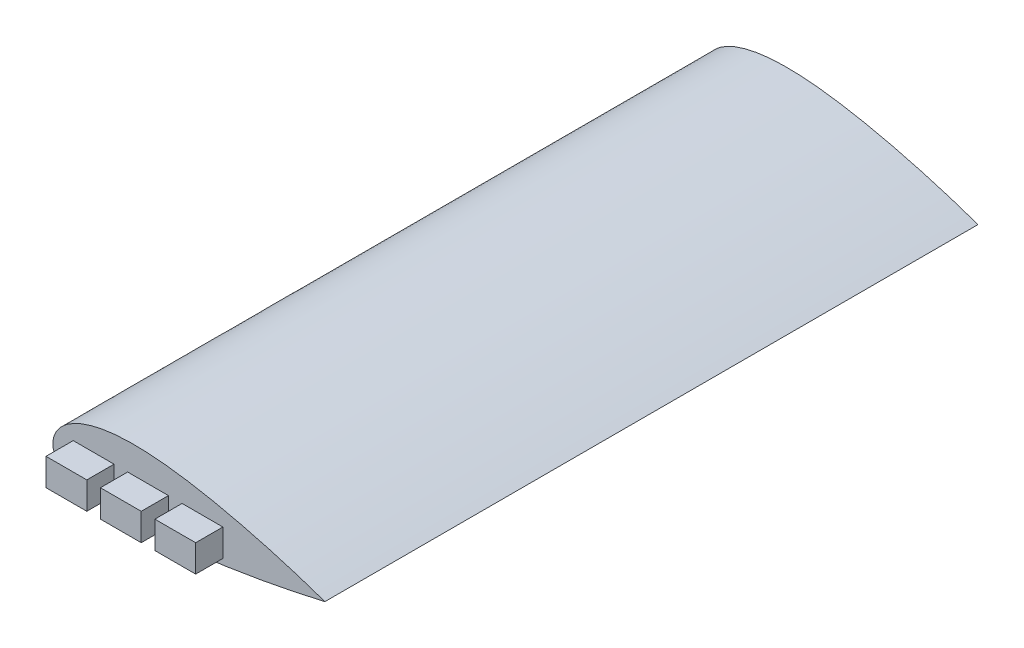
SolidWorks part; units mm, degrees
ref_plane "Front Plane" through (0, 0, 0) normal (0, 0, 1) x (1, 0, 0)
ref_plane "Top Plane" through (0, 0, 0) normal (0, 1, 0) x (1, 0, 0)
ref_plane "Right Plane" through (0, 0, 0) normal (1, 0, 0) x (0, 0, -1)
sketch "Sketch1" plane through (0, 0, 0) normal (0, 0, 1) x (1, 0, 0)
  spline S0 degree 4 poles (0, 0) (0.0009, 0.3297) (0.0295, 0.9275) (0.1439, 1.7967) (0.437, 2.9181) (0.8549, 3.9907) (1.4315, 5.0756) (2.1923, 6.1773) (3.2003, 7.33) (4.4959, 8.5106) (6.154, 9.7149) (8.2741, 10.9292) (10.957, 12.1146) (14.1477, 13.1525) (18.0405, 14.0363) (23.1343, 14.7366) (29.2357, 15.0274) (35.338, 14.8248) (41.1011, 14.3138) (46.841, 13.5968) (51.6037, 12.8505) (56.3456, 11.9834) (61.0671, 11.0139) (64.8328, 10.183) (68.5865, 9.3015) (72.3294, 8.3726) (76.0598, 7.3994) (79.3157, 6.5093) (82.096, 5.721) (84.4127, 5.0444) (86.2537, 4.4957) (88.1107, 3.9294) (89.9289, 3.3646) (91.806, 2.7666) (93.571, 2.1956) (95.5202, 1.5463) (97.1384, 1.0009) (99.1531, 0.3002) (100.3626, -0.127) (101.915, -0.6848) (103.1337, -1.1307) (104.3912, -1.5976) (105.6393, -2.0687) (106.8855, -2.5467) (108.1291, -3.0316) (109.0597, -3.4006) (109.6792, -3.6489) (109.9887, -3.7737) knots 0 0 0 0 0 0.011046 0.020082 0.029326 0.038802 0.04958 0.06121 0.074146 0.090071 0.108265 0.129827 0.155965 0.188307 0.220649 0.263591 0.328276 0.39296 0.425303 0.457645 0.522329 0.554672 0.587014 0.619356 0.651699 0.684041 0.716383 0.748725 0.764896 0.781068 0.797239 0.81341 0.829581 0.845752 0.861923 0.878094 0.894265 0.910437 0.921632 0.932827 0.944023 0.955218 0.966414 0.977609 0.988805 1 1 1 1 1 construction
  spline S1 degree 4 poles (0, 0) (0.0009, 0.3297) (0.0295, 0.9275) (0.1439, 1.7967) (0.437, 2.9181) (0.8549, 3.9907) (1.4315, 5.0756) (2.1923, 6.1773) (3.2003, 7.33) (4.4959, 8.5106) (6.154, 9.7149) (8.2741, 10.9292) (10.957, 12.1146) (14.1477, 13.1525) (18.0405, 14.0363) (23.1343, 14.7366) (29.2357, 15.0274) (35.338, 14.8248) (41.1011, 14.3138) (46.841, 13.5968) (51.6037, 12.8505) (56.3456, 11.9834) (61.0671, 11.0139) (64.8328, 10.183) (68.5865, 9.3015) (72.3294, 8.3726) (76.0598, 7.3994) (79.3157, 6.5093) (82.096, 5.721) (84.4127, 5.0444) (86.2537, 4.4957) (88.1107, 3.9294) (89.9289, 3.3646) (91.806, 2.7666) (93.571, 2.1956) (95.5202, 1.5463) (97.1383, 1.0009) (98.7751, 0.4317) (99.5867, 0.1465) (100.0002, 0) knots 0 0 0 0 0 0.011046 0.020082 0.029326 0.038802 0.04958 0.06121 0.074146 0.090071 0.108265 0.129827 0.155965 0.188307 0.220649 0.263591 0.328276 0.39296 0.425303 0.457645 0.522329 0.554672 0.587014 0.619356 0.651699 0.684041 0.716383 0.748725 0.764896 0.781068 0.797239 0.81341 0.829581 0.845752 0.861923 0.878094 0.894265 0.910434 0.910434 0.910434 0.910434 0.910434
  spline S2 degree 4 poles (0, 0) (0.0003, -0.1693) (0.016, -0.4614) (0.0775, -0.8851) (0.2333, -1.4356) (0.4512, -1.9609) (0.763, -2.5157) (1.1968, -3.1118) (1.8009, -3.7667) (2.6459, -4.4954) (3.845, -5.3152) (5.5202, -6.2106) (7.8905, -7.1807) (10.9471, -8.0963) (15.4296, -9.0396) (21.208, -9.73) (27.9775, -10.0275) (35.6486, -9.8891) (42.3469, -9.4657) (48.0748, -8.9399) (53.7915, -8.3061) (59.4968, -7.5766) (65.1885, -6.7461) (70.8667, -5.8302) (75.5899, -5.0142) (79.3624, -4.3307) (82.6596, -3.7058) (85.4801, -3.1515) (87.5962, -2.7233) (89.0005, -2.4341) (90.1811, -2.1872) (91.104, -1.9926) (92.3051, -1.7354) (93.6554, -1.4439) (95.3898, -1.0596) (97.1027, -0.6748) (99.4365, -0.1347) (101.1191, 0.2637) (103.9947, 0.9599) (105.7889, 1.4169) (107.9207, 1.9617) (109.0082, 2.2534) (109.6995, 2.4359) (109.9984, 2.5166) knots 0 0 0 0 0 0.005887 0.010193 0.014867 0.019889 0.025655 0.032315 0.040498 0.050865 0.064448 0.082823 0.106556 0.139954 0.175459 0.242256 0.309053 0.375849 0.442646 0.476045 0.509443 0.57624 0.643037 0.676435 0.709833 0.743232 0.77663 0.793329 0.810028 0.818378 0.826728 0.835077 0.843427 0.860126 0.876825 0.893524 0.910224 0.932668 0.955112 0.977556 0.988778 1 1 1 1 1 construction
  spline S3 degree 4 poles (0, 0) (0.0003, -0.1693) (0.016, -0.4614) (0.0775, -0.8851) (0.2333, -1.4356) (0.4512, -1.9609) (0.763, -2.5157) (1.1968, -3.1118) (1.8009, -3.7667) (2.6459, -4.4954) (3.845, -5.3152) (5.5202, -6.2106) (7.8905, -7.1807) (10.9471, -8.0963) (15.4296, -9.0396) (21.208, -9.73) (27.9775, -10.0275) (35.6486, -9.8891) (42.3469, -9.4657) (48.0748, -8.9399) (53.7915, -8.3061) (59.4968, -7.5766) (65.1885, -6.7461) (70.8667, -5.8302) (75.5899, -5.0142) (79.3624, -4.3307) (82.6596, -3.7058) (85.4801, -3.1515) (87.5962, -2.7233) (89.0005, -2.4341) (90.1811, -2.1872) (91.104, -1.9926) (92.3051, -1.7354) (93.6554, -1.4439) (95.3898, -1.0596) (97.1027, -0.6748) (98.7145, -0.3018) (99.5756, -0.1002) (100.0002, 0) knots 0 0 0 0 0 0.005887 0.010193 0.014867 0.019889 0.025655 0.032315 0.040498 0.050865 0.064448 0.082823 0.106556 0.139954 0.175459 0.242256 0.309053 0.375849 0.442646 0.476045 0.509443 0.57624 0.643037 0.676435 0.709833 0.743232 0.77663 0.793329 0.810028 0.818378 0.826728 0.835077 0.843427 0.860126 0.876825 0.893524 0.910224 0.910224 0.910224 0.910224 0.910224
sketch "Sketch2" plane through (0, 0, 0) normal (0, 1, 0) x (1, 0, 0)
  line L1 (0, 0) -> (0, -250) construction
  line L2 (0, -250) -> (50, -500) construction
  spline S0 degree 2 poles (0, 0) (0, -250) (50, -500) knots 0 0 0 1 1 1
  dimension "D1" = 250
  dimension "D2" = 250
  dimension "D3" = 50
ref_plane "Plane2" through (0, 0, 500) normal (0, 0, 1) x (1, 0, 0)
sketch "Sketch5" plane through (0, 0, 500) normal (0, 0, 1) x (1, 0, 0)
  spline S0 degree 4 poles (44.9961, 0) (44.997, 0.3297) (45.0257, 0.9275) (45.14, 1.7967) (45.4332, 2.9181) (45.851, 3.9907) (46.4276, 5.0756) (47.1884, 6.1773) (48.1965, 7.33) (49.4921, 8.5106) (51.1502, 9.7149) (53.2702, 10.9292) (55.9531, 12.1146) (59.1438, 13.1525) (63.0366, 14.0363) (68.1305, 14.7366) (74.2318, 15.0274) (80.3341, 14.8248) (86.0972, 14.3138) (91.8371, 13.5968) (96.5999, 12.8505) (101.3417, 11.9834) (106.0633, 11.0139) (109.8289, 10.183) (113.5826, 9.3015) (117.3256, 8.3726) (121.0559, 7.3994) (124.3119, 6.5093) (127.0921, 5.721) (129.4089, 5.0444) (131.2499, 4.4957) (133.1069, 3.9294) (134.9251, 3.3646) (136.8022, 2.7666) (138.5672, 2.1956) (140.5163, 1.5463) (142.1345, 1.0009) (144.1492, 0.3002) (145.3587, -0.127) (146.9111, -0.6848) (148.1299, -1.1307) (149.3874, -1.5976) (150.6354, -2.0687) (151.8817, -2.5467) (153.1253, -3.0316) (154.0559, -3.4006) (154.6753, -3.6489) (154.9848, -3.7737) knots 0 0 0 0 0 0.011046 0.020082 0.029326 0.038802 0.04958 0.06121 0.074146 0.090071 0.108265 0.129827 0.155965 0.188307 0.220649 0.263591 0.328276 0.39296 0.425303 0.457645 0.522329 0.554672 0.587014 0.619356 0.651699 0.684041 0.716383 0.748725 0.764896 0.781068 0.797239 0.81341 0.829581 0.845752 0.861923 0.878094 0.894265 0.910437 0.921632 0.932827 0.944023 0.955218 0.966414 0.977609 0.988805 1 1 1 1 1 construction
  spline S1 degree 4 poles (44.9961, 0) (44.997, 0.3297) (45.0257, 0.9275) (45.14, 1.7967) (45.4332, 2.9181) (45.851, 3.9907) (46.4276, 5.0756) (47.1884, 6.1773) (48.1965, 7.33) (49.4921, 8.5106) (51.1502, 9.7149) (53.2702, 10.9292) (55.9531, 12.1146) (59.1438, 13.1525) (63.0366, 14.0363) (68.1305, 14.7366) (74.2318, 15.0274) (80.3341, 14.8248) (86.0972, 14.3138) (91.8371, 13.5968) (96.5999, 12.8505) (101.3417, 11.9834) (106.0633, 11.0139) (109.8289, 10.183) (113.5826, 9.3015) (117.3256, 8.3726) (121.0559, 7.3994) (124.3119, 6.5093) (127.0921, 5.721) (129.4089, 5.0444) (131.2499, 4.4957) (133.1069, 3.9294) (134.9251, 3.3646) (136.8022, 2.7666) (138.5672, 2.1956) (140.5163, 1.5463) (142.1344, 1.0009) (143.7713, 0.4317) (144.5828, 0.1465) (144.9964, 0) knots 0 0 0 0 0 0.011046 0.020082 0.029326 0.038802 0.04958 0.06121 0.074146 0.090071 0.108265 0.129827 0.155965 0.188307 0.220649 0.263591 0.328276 0.39296 0.425303 0.457645 0.522329 0.554672 0.587014 0.619356 0.651699 0.684041 0.716383 0.748725 0.764896 0.781068 0.797239 0.81341 0.829581 0.845752 0.861923 0.878094 0.894265 0.910434 0.910434 0.910434 0.910434 0.910434 construction
  spline S2 degree 4 poles (44.9961, 0) (44.9964, -0.1693) (45.0121, -0.4614) (45.0736, -0.8851) (45.2294, -1.4356) (45.4474, -1.9609) (45.7592, -2.5157) (46.193, -3.1118) (46.7971, -3.7667) (47.642, -4.4954) (48.8411, -5.3152) (50.5163, -6.2106) (52.8866, -7.1807) (55.9432, -8.0963) (60.4257, -9.0396) (66.2041, -9.73) (72.9737, -10.0275) (80.6447, -9.8891) (87.343, -9.4657) (93.071, -8.9399) (98.7876, -8.3061) (104.493, -7.5766) (110.1846, -6.7461) (115.8628, -5.8302) (120.586, -5.0142) (124.3586, -4.3307) (127.6557, -3.7058) (130.4762, -3.1515) (132.5924, -2.7233) (133.9966, -2.4341) (135.1772, -2.1872) (136.1002, -1.9926) (137.3012, -1.7354) (138.6515, -1.4439) (140.3859, -1.0596) (142.0988, -0.6748) (144.4327, -0.1347) (146.1152, 0.2637) (148.9908, 0.9599) (150.7851, 1.4169) (152.9168, 1.9617) (154.0043, 2.2534) (154.6957, 2.4359) (154.9945, 2.5166) knots 0 0 0 0 0 0.005887 0.010193 0.014867 0.019889 0.025655 0.032315 0.040498 0.050865 0.064448 0.082823 0.106556 0.139954 0.175459 0.242256 0.309053 0.375849 0.442646 0.476045 0.509443 0.57624 0.643037 0.676435 0.709833 0.743232 0.77663 0.793329 0.810028 0.818378 0.826728 0.835077 0.843427 0.860126 0.876825 0.893524 0.910224 0.932668 0.955112 0.977556 0.988778 1 1 1 1 1 construction
  spline S3 degree 4 poles (44.9961, 0) (44.9964, -0.1693) (45.0121, -0.4614) (45.0736, -0.8851) (45.2294, -1.4356) (45.4474, -1.9609) (45.7592, -2.5157) (46.193, -3.1118) (46.7971, -3.7667) (47.642, -4.4954) (48.8411, -5.3152) (50.5163, -6.2106) (52.8866, -7.1807) (55.9432, -8.0963) (60.4257, -9.0396) (66.2041, -9.73) (72.9737, -10.0275) (80.6447, -9.8891) (87.343, -9.4657) (93.071, -8.9399) (98.7876, -8.3061) (104.493, -7.5766) (110.1846, -6.7461) (115.8628, -5.8302) (120.586, -5.0142) (124.3586, -4.3307) (127.6557, -3.7058) (130.4762, -3.1515) (132.5924, -2.7233) (133.9966, -2.4341) (135.1772, -2.1872) (136.1002, -1.9926) (137.3012, -1.7354) (138.6515, -1.4439) (140.3859, -1.0596) (142.0988, -0.6748) (143.7106, -0.3018) (144.5718, -0.1002) (144.9964, 0) knots 0 0 0 0 0 0.005887 0.010193 0.014867 0.019889 0.025655 0.032315 0.040498 0.050865 0.064448 0.082823 0.106556 0.139954 0.175459 0.242256 0.309053 0.375849 0.442646 0.476045 0.509443 0.57624 0.643037 0.676435 0.709833 0.743232 0.77663 0.793329 0.810028 0.818378 0.826728 0.835077 0.843427 0.860126 0.876825 0.893524 0.910224 0.910224 0.910224 0.910224 0.910224 construction
  spline S4 degree 1 poles (50, 0.1659) (125.4884, 0.9751) knots 0 0 1 1 construction
  spline S5 degree 1 poles (50, 0.1659) (125.4884, 0.9751) knots 0 0 1 1 construction
  spline S6 degree 3 poles (50, 0.1659) (50.0179, 0.6032) (50.1757, 1.4567) (50.8242, 2.7316) (51.9666, 4.0552) (54.0561, 5.71) (57.4359, 7.406) (62.0985, 8.7726) (67.0831, 9.581) (73.966, 10.0492) (82.8075, 9.7192) (93.5157, 8.3656) (107.7971, 5.6881) (118.4649, 2.9873) (125.4884, 0.9751) knots 0.003107 0.003107 0.003107 0.003107 0.026472 0.049837 0.073202 0.096568 0.143298 0.190028 0.236758 0.283489 0.376949 0.47041 0.56387 0.750791 0.750791 0.750791 0.750791
  spline S7 degree 3 poles (125.4884, 0.9751) (118.8048, -0.2943) (108.7202, -1.9955) (95.2701, -3.722) (85.1977, -4.6498) (76.8507, -4.9962) (70.2537, -4.8947) (65.3724, -4.5831) (61.4032, -4.0773) (58.338, -3.4825) (56.1227, -2.928) (54.0329, -2.2507) (52.4618, -1.576) (51.3904, -0.9852) (50.7151, -0.5321) (50.3053, -0.1828) (50.0857, 0.053) (50.0309, 0.1225) (50, 0.1659) knots 0.025551 0.025551 0.025551 0.025551 0.205368 0.295277 0.385186 0.475094 0.520049 0.565003 0.609957 0.632435 0.654912 0.677389 0.699866 0.711105 0.722343 0.733582 0.739201 0.74482 0.74482 0.74482 0.74482
  spline S8 degree 1 poles (57.6356, 1.8665) (100.2923, 1.9767) knots 0 0 1 1 construction
  spline S9 degree 1 poles (57.6356, 1.8665) (100.2923, 1.9767) knots 0 0 1 1 construction
  spline S10 degree 3 poles (57.6356, 1.8665) (57.9231, 2.0151) (58.4925, 2.2874) (59.782, 2.82) (61.5543, 3.4029) (63.8869, 3.9672) (67.1912, 4.5347) (71.5938, 4.9175) (77.127, 4.9346) (82.8116, 4.5908) (88.5912, 3.9528) (94.4204, 3.0772) (98.3432, 2.3598) (100.2923, 1.9767) knots 0.118651 0.118651 0.118651 0.118651 0.131754 0.144858 0.171065 0.197272 0.223479 0.275893 0.328307 0.380721 0.433135 0.485549 0.537964 0.537964 0.537964 0.537964
  spline S11 degree 3 poles (100.2923, 1.9767) (98.4159, 1.7345) (94.6502, 1.2813) (87.1702, 0.537) (79.7557, 0.0753) (72.5111, 0.0364) (68.0926, 0.2319) (64.6731, 0.551) (62.1863, 0.8819) (60.2071, 1.2401) (58.6967, 1.5822) (57.9917, 1.7662) (57.6356, 1.8665) knots 0.116889 0.116889 0.116889 0.116889 0.167972 0.219056 0.321223 0.372307 0.42339 0.448932 0.474474 0.500016 0.512787 0.525558 0.525558 0.525558 0.525558
  dimension "D1" = 5
  dimension "D3" = 50
  dimension "D2" = 10
sketch "Sketch6" plane through (0, 0, 0) normal (0, 0, 1) x (1, 0, 0)
  spline S0 degree 4 poles (0, 0) (0.0009, 0.3297) (0.0295, 0.9275) (0.1439, 1.7967) (0.437, 2.9181) (0.8549, 3.9907) (1.4315, 5.0756) (2.1923, 6.1773) (3.2003, 7.33) (4.4959, 8.5106) (6.154, 9.7149) (8.2741, 10.9292) (10.957, 12.1146) (14.1477, 13.1525) (18.0405, 14.0363) (23.1343, 14.7366) (29.2357, 15.0274) (35.338, 14.8248) (41.1011, 14.3138) (46.841, 13.5968) (51.6037, 12.8505) (56.3456, 11.9834) (61.0671, 11.0139) (64.8328, 10.183) (68.5865, 9.3015) (72.3294, 8.3726) (76.0598, 7.3994) (79.3157, 6.5093) (82.096, 5.721) (84.4127, 5.0444) (86.2537, 4.4957) (88.1107, 3.9294) (89.9289, 3.3646) (91.806, 2.7666) (93.571, 2.1956) (95.5202, 1.5463) (97.1384, 1.0009) (99.1531, 0.3002) (100.3626, -0.127) (101.915, -0.6848) (103.1337, -1.1307) (104.3912, -1.5976) (105.6393, -2.0687) (106.8855, -2.5467) (108.1291, -3.0316) (109.0597, -3.4006) (109.6792, -3.6489) (109.9887, -3.7737) knots 0 0 0 0 0 0.011046 0.020082 0.029326 0.038802 0.04958 0.06121 0.074146 0.090071 0.108265 0.129827 0.155965 0.188307 0.220649 0.263591 0.328276 0.39296 0.425303 0.457645 0.522329 0.554672 0.587014 0.619356 0.651699 0.684041 0.716383 0.748725 0.764896 0.781068 0.797239 0.81341 0.829581 0.845752 0.861923 0.878094 0.894265 0.910437 0.921632 0.932827 0.944023 0.955218 0.966414 0.977609 0.988805 1 1 1 1 1 construction
  spline S1 degree 4 poles (0, 0) (0.0009, 0.3297) (0.0295, 0.9275) (0.1439, 1.7967) (0.437, 2.9181) (0.8549, 3.9907) (1.4315, 5.0756) (2.1923, 6.1773) (3.2003, 7.33) (4.4959, 8.5106) (6.154, 9.7149) (8.2741, 10.9292) (10.957, 12.1146) (14.1477, 13.1525) (18.0405, 14.0363) (23.1343, 14.7366) (29.2357, 15.0274) (35.338, 14.8248) (41.1011, 14.3138) (46.841, 13.5968) (51.6037, 12.8505) (56.3456, 11.9834) (61.0671, 11.0139) (64.8328, 10.183) (68.5865, 9.3015) (72.3294, 8.3726) (76.0598, 7.3994) (79.3157, 6.5093) (82.096, 5.721) (84.4127, 5.0444) (86.2537, 4.4957) (88.1107, 3.9294) (89.9289, 3.3646) (91.806, 2.7666) (93.571, 2.1956) (95.5202, 1.5463) (97.1383, 1.0009) (98.7751, 0.4317) (99.5867, 0.1465) (100.0002, 0) knots 0 0 0 0 0 0.011046 0.020082 0.029326 0.038802 0.04958 0.06121 0.074146 0.090071 0.108265 0.129827 0.155965 0.188307 0.220649 0.263591 0.328276 0.39296 0.425303 0.457645 0.522329 0.554672 0.587014 0.619356 0.651699 0.684041 0.716383 0.748725 0.764896 0.781068 0.797239 0.81341 0.829581 0.845752 0.861923 0.878094 0.894265 0.910434 0.910434 0.910434 0.910434 0.910434 construction
  spline S2 degree 4 poles (0, 0) (0.0003, -0.1693) (0.016, -0.4614) (0.0775, -0.8851) (0.2333, -1.4356) (0.4512, -1.9609) (0.763, -2.5157) (1.1968, -3.1118) (1.8009, -3.7667) (2.6459, -4.4954) (3.845, -5.3152) (5.5202, -6.2106) (7.8905, -7.1807) (10.9471, -8.0963) (15.4296, -9.0396) (21.208, -9.73) (27.9775, -10.0275) (35.6486, -9.8891) (42.3469, -9.4657) (48.0748, -8.9399) (53.7915, -8.3061) (59.4968, -7.5766) (65.1885, -6.7461) (70.8667, -5.8302) (75.5899, -5.0142) (79.3624, -4.3307) (82.6596, -3.7058) (85.4801, -3.1515) (87.5962, -2.7233) (89.0005, -2.4341) (90.1811, -2.1872) (91.104, -1.9926) (92.3051, -1.7354) (93.6554, -1.4439) (95.3898, -1.0596) (97.1027, -0.6748) (99.4365, -0.1347) (101.1191, 0.2637) (103.9947, 0.9599) (105.7889, 1.4169) (107.9207, 1.9617) (109.0082, 2.2534) (109.6995, 2.4359) (109.9984, 2.5166) knots 0 0 0 0 0 0.005887 0.010193 0.014867 0.019889 0.025655 0.032315 0.040498 0.050865 0.064448 0.082823 0.106556 0.139954 0.175459 0.242256 0.309053 0.375849 0.442646 0.476045 0.509443 0.57624 0.643037 0.676435 0.709833 0.743232 0.77663 0.793329 0.810028 0.818378 0.826728 0.835077 0.843427 0.860126 0.876825 0.893524 0.910224 0.932668 0.955112 0.977556 0.988778 1 1 1 1 1 construction
  spline S3 degree 4 poles (0, 0) (0.0003, -0.1693) (0.016, -0.4614) (0.0775, -0.8851) (0.2333, -1.4356) (0.4512, -1.9609) (0.763, -2.5157) (1.1968, -3.1118) (1.8009, -3.7667) (2.6459, -4.4954) (3.845, -5.3152) (5.5202, -6.2106) (7.8905, -7.1807) (10.9471, -8.0963) (15.4296, -9.0396) (21.208, -9.73) (27.9775, -10.0275) (35.6486, -9.8891) (42.3469, -9.4657) (48.0748, -8.9399) (53.7915, -8.3061) (59.4968, -7.5766) (65.1885, -6.7461) (70.8667, -5.8302) (75.5899, -5.0142) (79.3624, -4.3307) (82.6596, -3.7058) (85.4801, -3.1515) (87.5962, -2.7233) (89.0005, -2.4341) (90.1811, -2.1872) (91.104, -1.9926) (92.3051, -1.7354) (93.6554, -1.4439) (95.3898, -1.0596) (97.1027, -0.6748) (98.7145, -0.3018) (99.5756, -0.1002) (100.0002, 0) knots 0 0 0 0 0 0.005887 0.010193 0.014867 0.019889 0.025655 0.032315 0.040498 0.050865 0.064448 0.082823 0.106556 0.139954 0.175459 0.242256 0.309053 0.375849 0.442646 0.476045 0.509443 0.57624 0.643037 0.676435 0.709833 0.743232 0.77663 0.793329 0.810028 0.818378 0.826728 0.835077 0.843427 0.860126 0.876825 0.893524 0.910224 0.910224 0.910224 0.910224 0.910224 construction
  spline S4 degree 1 poles (5.0039, 0.1659) (80.4922, 0.9751) knots 0 0 1 1 construction
  spline S5 degree 1 poles (5.0039, 0.1659) (80.4922, 0.9751) knots 0 0 1 1 construction
  spline S6 degree 3 poles (5.0039, 0.1659) (5.0218, 0.6032) (5.1796, 1.4567) (5.8281, 2.7316) (6.9704, 4.0552) (9.0599, 5.71) (12.4398, 7.406) (17.1024, 8.7726) (22.0869, 9.581) (28.9699, 10.0492) (37.8114, 9.7192) (48.5196, 8.3656) (62.801, 5.6881) (73.4687, 2.9873) (80.4922, 0.9751) knots 0.003107 0.003107 0.003107 0.003107 0.026472 0.049837 0.073202 0.096568 0.143298 0.190028 0.236758 0.283489 0.376949 0.47041 0.56387 0.750791 0.750791 0.750791 0.750791
  spline S7 degree 3 poles (80.4922, 0.9751) (73.8087, -0.2943) (63.7241, -1.9955) (50.274, -3.722) (40.2016, -4.6498) (31.8546, -4.9962) (25.2576, -4.8947) (20.3763, -4.5831) (16.407, -4.0773) (13.3418, -3.4825) (11.1266, -2.928) (9.0368, -2.2507) (7.4657, -1.576) (6.3942, -0.9852) (5.719, -0.5321) (5.3091, -0.1828) (5.0896, 0.053) (5.0347, 0.1225) (5.0039, 0.1659) knots 0.025551 0.025551 0.025551 0.025551 0.205368 0.295277 0.385186 0.475094 0.520049 0.565003 0.609957 0.632435 0.654912 0.677389 0.699866 0.711105 0.722343 0.733582 0.739201 0.74482 0.74482 0.74482 0.74482
  dimension "D1" = 5
extrude "Boss-Extrude1" add sketch "Sketch1" along normal mid plane 250
extrude "Cut-Extrude1" cut sketch "Sketch6" against normal blind 120 and the other way blind 110
sketch "Sketch8" plane through (0, 0, 125) normal (0, 0, 1) x (1, 0, 0)
  line L1 (27.5, -5) -> (42.5, -5)
  line L2 (27.5, -5) -> (27.5, 5)
  line L3 (27.5, 5) -> (42.5, 5)
  line L4 (42.5, -5) -> (42.5, 5)
  line L5 (22.5, 5) -> (7.5, 5)
  line L6 (22.5, 5) -> (22.5, -5)
  line L7 (22.5, -5) -> (7.5, -5)
  line L8 (7.5, 5) -> (7.5, -5)
  line L9 (47.5, 5) -> (62.5, 5)
  line L10 (47.5, 5) -> (47.5, -5)
  line L11 (47.5, -5) -> (62.5, -5)
  line L12 (62.5, 5) -> (62.5, -5)
  point P6 (7.5, 0)
  point P7 (27.5, 0)
  point P17 (35, 5)
  point P18 (47.5, 0)
  dimension "D1" = 35
  dimension "D2" = 15
  dimension "D3" = 10
  dimension "D4" = 15
  dimension "D5" = 10
  dimension "D6" = 5
  dimension "D7" = 15
  dimension "D8" = 10
  dimension "D9" = 5
extrude "Cut-Extrude2" cut sketch "Sketch8" against normal blind 10 flip side to cut
